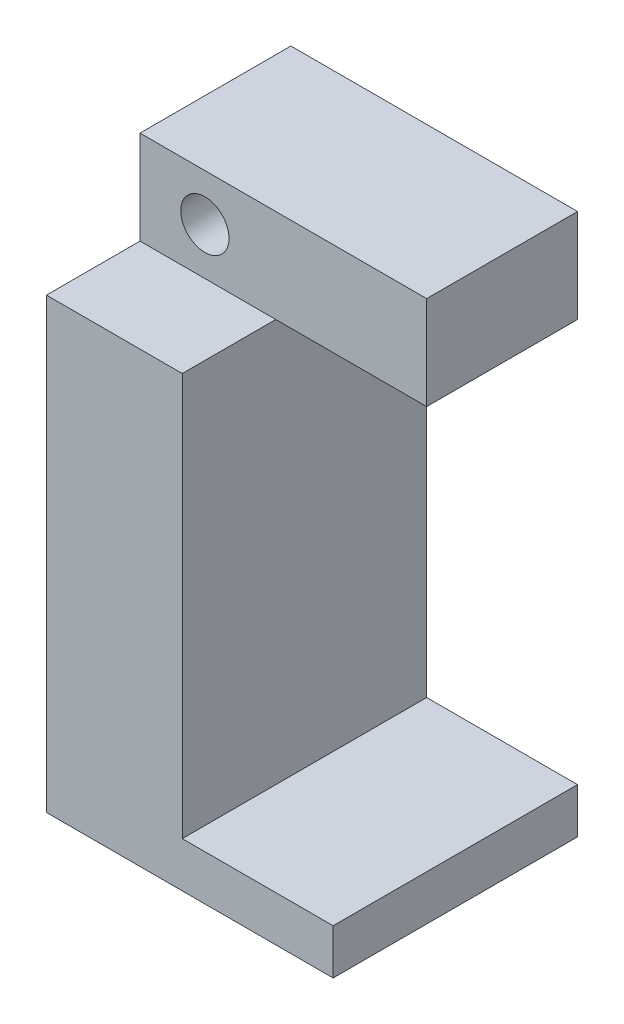
SolidWorks part; units mm, degrees
ref_plane "Alzado" through (0, 0, 0) normal (0, 0, 1) x (1, 0, 0)
ref_plane "Planta" through (0, 0, 0) normal (0, 1, 0) x (1, 0, 0)
ref_plane "Vista lateral" through (0, 0, 0) normal (1, 0, 0) x (0, 0, -1)
sketch "Croquis1" plane through (0, 0, 0) normal (0, 0, 1) x (1, 0, 0)
  line L0 (0, 0) -> (19, 0)
  line L1 (19, 0) -> (19, 3)
  line L2 (19, 3) -> (9, 3)
  line L3 (9, 3) -> (9, 29.7)
  line L4 (9, 29.7) -> (19, 29.7)
  line L5 (19, 29.7) -> (19, 35.9)
  line L6 (19, 35.9) -> (0, 35.9)
  line L7 (0, 35.9) -> (0, 0)
  dimension "D1" = 3
  dimension "D2" = 26.7
  dimension "D3" = 6.2
  dimension "D4" = 19
  dimension "D5" = 10
extrude "Saliente-Extruir1" add sketch "Croquis1" along normal blind 10
sketch "Croquis2" plane through (0, 0, 10) normal (0, 0, 1) x (1, 0, 0)
  line L0 (9, 29.7) -> (0, 29.7)
  line L8 (0, 35.9) -> (0, 0)
  line L9 (0, 0) -> (19, 0)
  line L10 (19, 0) -> (19, 3)
  line L11 (19, 3) -> (9, 3)
  line L12 (9, 3) -> (9, 29.7)
  line L13 (9, 29.7) -> (19, 29.7)
  line L14 (19, 29.7) -> (19, 35.9)
  line L15 (19, 35.9) -> (0, 35.9)
  line L16 (0, 29.7) -> (0, 0)
  line L17 (0, 0) -> (19, 0)
  line L18 (19, 0) -> (19, 3)
  line L19 (19, 3) -> (9, 3)
  line L20 (9, 3) -> (9, 29.7)
  dimension "D1" = 0
extrude "Saliente-Extruir2" add sketch "Croquis2" along normal blind 6.2
sketch "Croquis3" plane through (0, 0, 10) normal (0, 0, 1) x (1, 0, 0)
  line L0 (9, 29.7) -> (9, 32.8) construction
  line L1 (9, 32.8) -> (4.3, 32.8) construction
  circle A0 centre (4.3, 32.8) radius 1.6
  dimension "D3" = 3.2
  dimension "D1" = 4.7
  dimension "D2" = 3.1
extrude "Cortar-Extruir1" cut sketch "Croquis3" against normal up to next
sketch "Croquis4" plane through (0, 0, 0) normal (0, 0, -1) x (-1, 0, 0)
  line L1 (-2.6546, 35.65) -> (-5.9454, 35.65)
  line L2 (-5.9454, 35.65) -> (-7.5909, 32.8)
  line L3 (-7.5909, 32.8) -> (-5.9454, 29.95)
  line L4 (-5.9454, 29.95) -> (-2.6546, 29.95)
  line L5 (-2.6546, 29.95) -> (-1.0091, 32.8)
  line L6 (-1.0091, 32.8) -> (-2.6546, 35.65)
  circle A0 centre (-4.3, 32.8) radius 2.85 construction
  dimension "D1" = 5.7
extrude "Cortar-Extruir2" cut sketch "Croquis4" against normal blind 3
